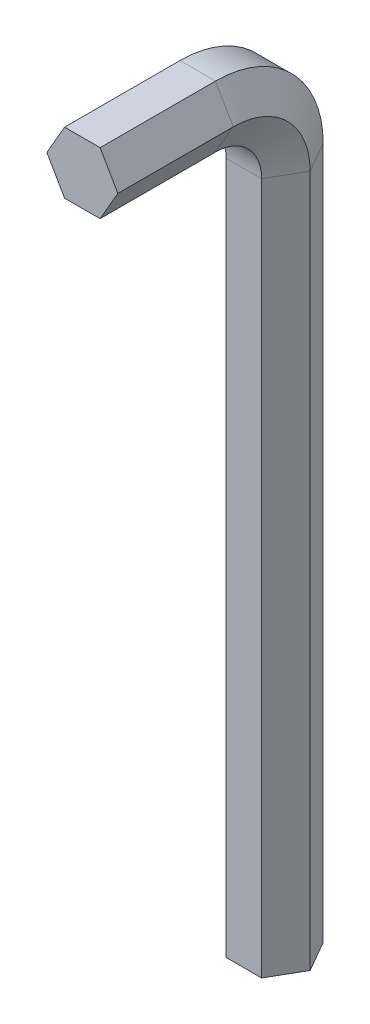
SolidWorks part; units mm, degrees
ref_plane "Přední rovina" through (0, 0, 0) normal (0, 0, 1) x (1, 0, 0)
ref_plane "Vrchní rovina" through (0, 0, 0) normal (0, 1, 0) x (1, 0, 0)
ref_plane "Pravá rovina" through (0, 0, 0) normal (1, 0, 0) x (0, 0, -1)
sketch "Skica2" plane through (0, 0, 0) normal (0, 1, 0) x (1, 0, 0)
  line L1 (2.3094, -4) -> (4.6188, 0)
  line L2 (4.6188, 0) -> (2.3094, 4)
  line L3 (2.3094, 4) -> (-2.3094, 4)
  line L4 (-2.3094, 4) -> (-4.6188, 0)
  line L5 (-4.6188, 0) -> (-2.3094, -4)
  line L6 (-2.3094, -4) -> (2.3094, -4)
  circle A0 centre (0, 0) radius 4 construction
  dimension "s" = 8
sketch "Skica4" plane through (0, 0, 0) normal (1, 0, 0) x (0, 0, -1)
  line L0 (0, 0) -> (0, 90)
  line L1 (-10, 100) -> (-25, 100)
  arc A0 (0, 90) -> (-10, 100) centre (-10, 90) ccw
  dimension "R" = 10
  dimension "A" = 100
  dimension "B" = 25
sweep "Táhnout po křivce1" add profiles "Skica2" path "Skica4"
